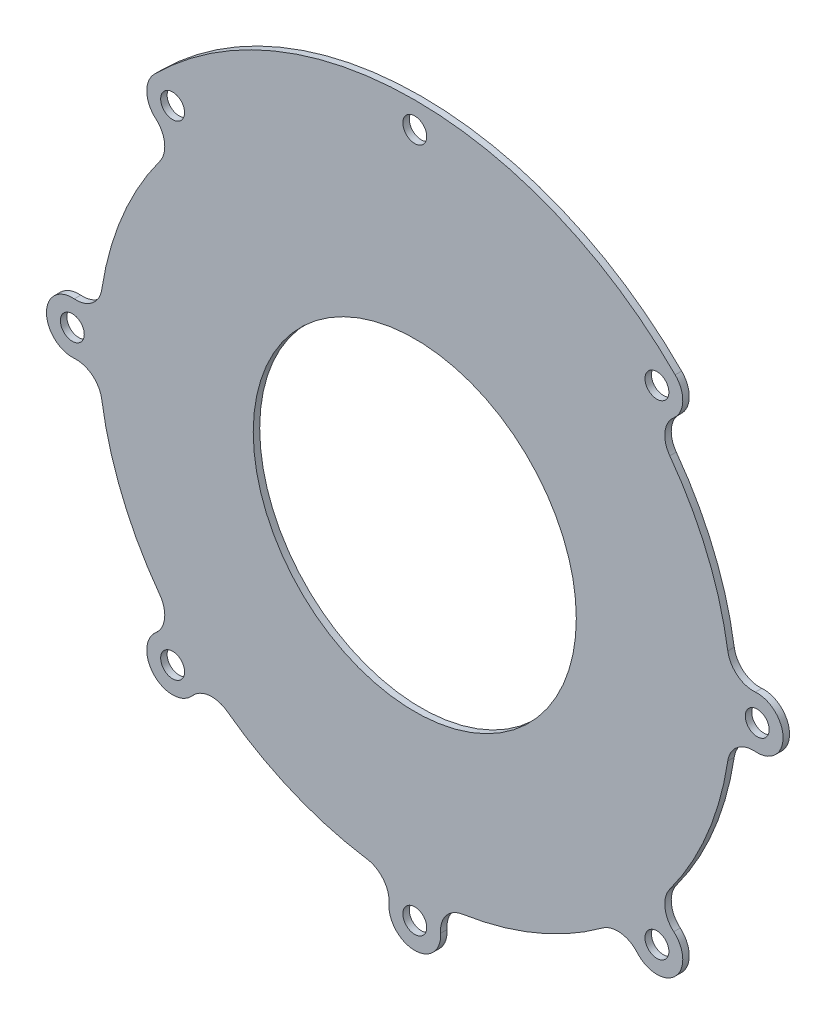
SolidWorks part; units mm, degrees
material "FR4"
ref_plane "Ön Düzlem" through (0, 0, 0) normal (0, 0, 1) x (1, 0, 0)
ref_plane "Üst Düzlem" through (0, 0, 0) normal (0, 1, 0) x (1, 0, 0)
ref_plane "Sağ Düzlem" through (0, 0, 0) normal (1, 0, 0) x (0, 0, -1)
sketch "NPTH" plane through (0, 0, 0) normal (0, 0, 1) x (1, 0, 0)
  circle A0 centre (0, 0) radius 25
  arc A1 (-39.4685, 29.0385) -> (-48.4418, 7.3751) centre (0, 0) ccw
  arc A2 (40.3051, 40.3051) -> (-40.3051, 40.3051) centre (0, 0) ccw
  circle A3 centre (0, -53) radius 1.85
  circle A4 centre (0, 0) radius 53 construction
  arc A5 (-3.9886, -52.6981) -> (3.9886, -52.6981) centre (0, -53) ccw
  arc A6 (7.3751, -48.4418) -> (4.0028, -52.8486) centre (7.9772, -52.3962) ccw
  arc A7 (-4.0028, -52.8486) -> (-7.3751, -48.4418) centre (-7.9772, -52.3962) ccw
  arc A8 (-29.0385, -39.4685) -> (-34.5392, -40.2001) centre (-31.409, -42.6904) ccw
  circle A9 centre (-37.4767, -37.4767) radius 1.85
  arc A10 (-40.0836, -34.4428) -> (-34.4428, -40.0836) centre (-37.4767, -37.4767) ccw
  arc A11 (-40.2001, -34.5392) -> (-39.4685, -29.0385) centre (-42.6904, -31.409) ccw
  arc A12 (-48.4418, -7.3751) -> (-52.8486, -4.0028) centre (-52.3962, -7.9772) ccw
  circle A13 centre (-53, 0) radius 1.85
  arc A14 (-52.6981, 3.9886) -> (-52.6981, -3.9886) centre (-53, 0) ccw
  arc A15 (-52.8486, 4.0028) -> (-48.4418, 7.3751) centre (-52.3962, 7.9772) ccw
  arc A16 (-39.4685, 29.0385) -> (-40.2001, 34.5392) centre (-42.6904, 31.409) ccw
  circle A17 centre (-37.4767, 37.4767) radius 1.85
  arc A18 (-40.3051, 40.3051) -> (-40.0836, 34.4428) centre (-37.4767, 37.4767) ccw
  circle A21 centre (0, 53) radius 1.85
  circle A25 centre (37.4767, 37.4767) radius 1.85
  arc A26 (40.0836, 34.4428) -> (40.3051, 40.3051) centre (37.4767, 37.4767) ccw
  arc A27 (40.2001, 34.5392) -> (39.4685, 29.0385) centre (42.6904, 31.409) ccw
  arc A28 (48.4418, 7.3751) -> (52.8486, 4.0028) centre (52.3962, 7.9772) ccw
  circle A29 centre (53, 0) radius 1.85
  arc A30 (52.6981, -3.9886) -> (52.6981, 3.9886) centre (53, 0) ccw
  arc A31 (52.8486, -4.0028) -> (48.4418, -7.3751) centre (52.3962, -7.9772) ccw
  arc A32 (39.4685, -29.0385) -> (40.2001, -34.5392) centre (42.6904, -31.409) ccw
  circle A33 centre (37.4767, -37.4767) radius 1.85
  arc A34 (34.4428, -40.0836) -> (40.0836, -34.4428) centre (37.4767, -37.4767) ccw
  arc A35 (34.5392, -40.2001) -> (29.0385, -39.4685) centre (31.409, -42.6904) ccw
  arc A36 (7.3751, -48.4418) -> (29.0385, -39.4685) centre (0, 0) ccw
  arc A37 (39.4685, -29.0385) -> (48.4418, -7.3751) centre (0, 0) ccw
  arc A38 (33.7795, 45.9124) -> (28.0999, 44.9377) centre (31.409, 42.6904) ccw [skipped]
  circle A39 centre (0, 53) radius 4 [skipped]
  circle A40 centre (7.9772, 52.3962) radius 4 [skipped]
  circle A41 centre (-7.9772, 52.3962) radius 4 [skipped]
  circle A42 centre (-31.409, 42.6904) radius 4 [skipped]
  arc A43 (-29.0385, -39.4685) -> (-7.3751, -48.4418) centre (0, 0) ccw
  arc A44 (48.4418, 7.3751) -> (39.4685, 29.0385) centre (0, 0) ccw
  arc A45 (-48.4418, -7.3751) -> (-39.4685, -29.0385) centre (0, 0) ccw
  point P72 (0, 0)
  dimension "D1" = 50
  dimension "D2" = 98
  dimension "D3" = 114
  dimension "D4" = 3.7
  dimension "D5" = 106
  dimension "D6" = 8
  dimension "D7" = 8
extrude "Boss-Extrude1" add sketch "NPTH" along normal blind 1 contours A12 A45 A11 A10 A8 A43 A7 A5 A6 A36 A35 A34 A32 A37 A31 A30 A28 A44 A27 A26 A2 A18 A16 A1 A15 A14 A0 A3 A9 A13 A17 A21 A25 A29 A33
